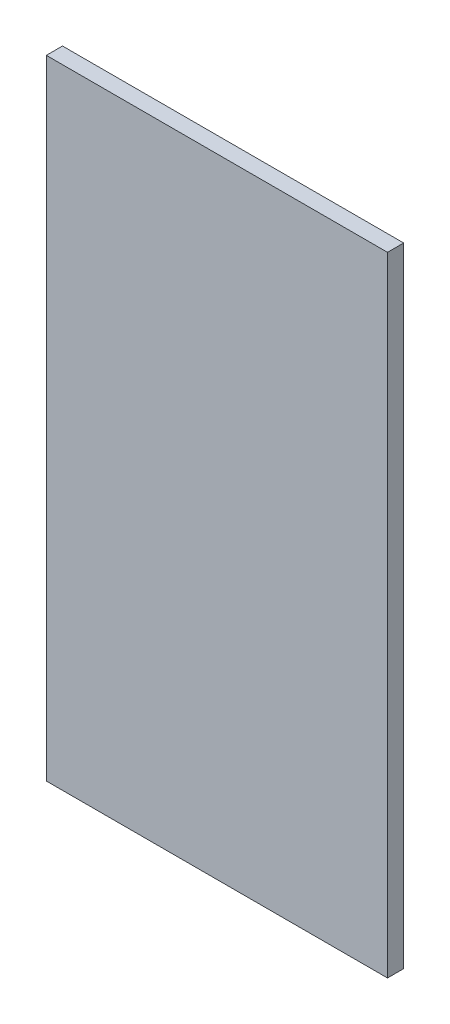
SolidWorks part; units mm, degrees
ref_plane "Front Plane" through (0, 0, 0) normal (0, 0, 1) x (1, 0, 0)
ref_plane "Top Plane" through (0, 0, 0) normal (0, 1, 0) x (1, 0, 0)
ref_plane "Right Plane" through (0, 0, 0) normal (1, 0, 0) x (0, 0, -1)
sketch "Sketch1" plane through (0, 0, 0) normal (0, 0, 1) x (1, 0, 0)
  line L1 (-25.3833, -32.476) -> (354.6167, -32.476)
  line L2 (-25.3833, -32.476) -> (-25.3833, 667.524)
  line L3 (-25.3833, 667.524) -> (354.6167, 667.524)
  line L4 (354.6167, -32.476) -> (354.6167, 667.524)
  dimension "D1" = 700
  dimension "D2" = 380
extrude "Boss-Extrude1" add sketch "Sketch1" along normal blind 18
